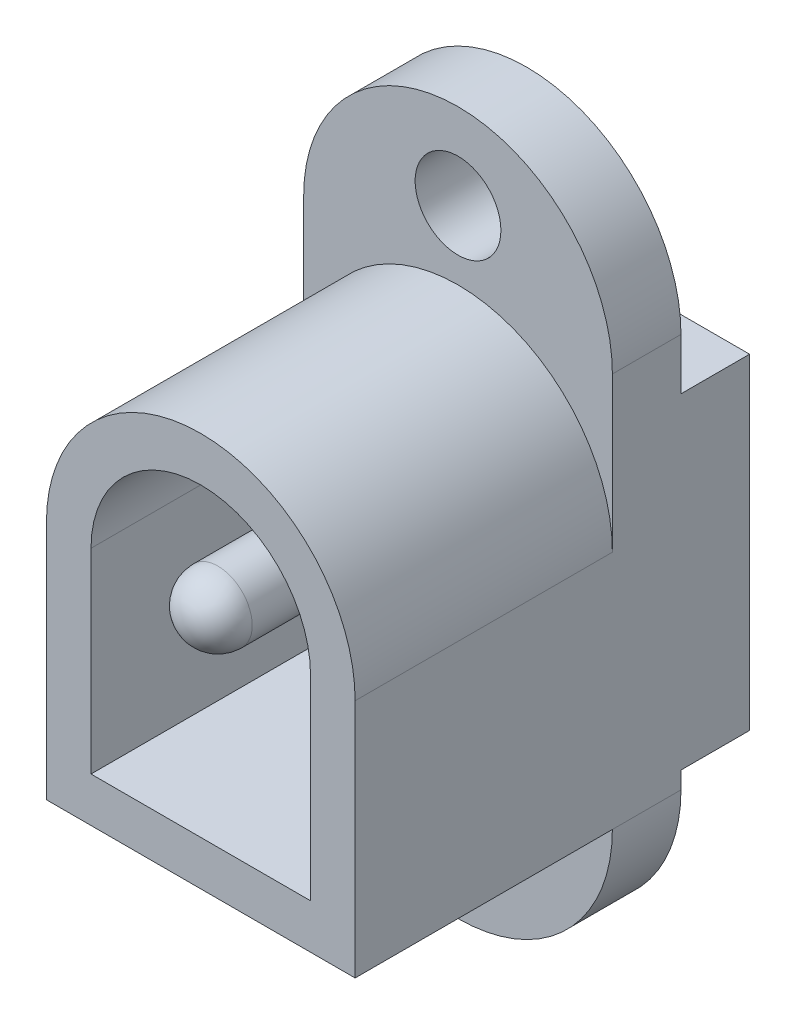
SolidWorks part; units mm, degrees
ref_plane "Piano frontale" through (0, 0, 0) normal (0, 0, 1) x (1, 0, 0)
ref_plane "Piano superiore" through (0, 0, 0) normal (0, 1, 0) x (1, 0, 0)
ref_plane "Piano destro" through (0, 0, 0) normal (1, 0, 0) x (0, 0, -1)
sketch "Schizzo1" plane through (0, 0, 0) normal (0, 0, 1) x (1, 0, 0)
  line L1 (4.5, -5.75) -> (-4.5, -5.75)
  line L2 (4.5, -5.75) -> (4.5, 5.75)
  line L3 (4.5, 5.75) -> (-4.5, 5.75)
  line L4 (-4.5, -5.75) -> (-4.5, 5.75)
  line L5 (4.5, -5.75) -> (-4.5, 5.75) construction
  line L6 (4.5, 5.75) -> (-4.5, -5.75) construction
  point P0 (0, 0)
  dimension "D1" = 9
  dimension "D2" = 11.5
extrude "Estrusione-Estrusione1" add sketch "Schizzo1" along normal blind 2
sketch "Schizzo2" plane through (0, 0, 2) normal (0, 0, 1) x (1, 0, 0)
  line L0 (0, 5.75) -> (0, -5.75) construction
  line L1 (4.5, 5.75) -> (-4.5, 5.75) construction
  line L2 (-4.5, -5.75) -> (4.5, -5.75) construction
  circle A0 centre (0, 5.75) radius 4.5
  circle A1 centre (0, -5.75) radius 4.5
extrude "Estrusione-Estrusione2" add sketch "Schizzo2" against normal blind 2
sketch "Schizzo3" plane through (0, 0, 2) normal (0, 0, 1) x (1, 0, 0)
  line L0 (0, 10.25) -> (0, -10.25) construction
  arc A0 (4.5, 5.75) -> (-4.5, 5.75) centre (0, 5.75) ccw construction
  arc A1 (-4.5, -5.75) -> (4.5, -5.75) centre (0, -5.75) ccw construction
  circle A2 centre (0, -7.75) radius 1.25
  circle A3 centre (0, 7.75) radius 1.25
  dimension "D3" = 2.5
  dimension "D4" = 2.5
  dimension "D1" = 7.75
  dimension "D2" = 7.75
extrude "Taglio-Estrusione1" cut sketch "Schizzo3" against normal blind 2
sketch "Schizzo4" plane through (0, 0, 2) normal (0, 0, 1) x (1, 0, 0)
  line L0 (-4.5, -5.75) -> (4.5, -5.75)
  line L1 (4.5, -5.75) -> (4.5, 1.25)
  line L2 (4.5, -5.75) -> (4.5, 5.75) construction
  line L3 (4.5, 1.25) -> (-4.5, 1.25)
  line L4 (-4.5, 5.75) -> (-4.5, -5.75) construction
  line L5 (-4.5, 1.25) -> (-4.5, -5.75)
  line L6 (-4.5, 1.25) -> (-4.5, -5.75)
  circle A0 centre (0, 1.25) radius 4.5
  line M3 (-4.5, 5.75) -> (-4.5, -5.75)
  line M5 (4.5, -5.75) -> (4.5, 5.75)
  dimension "D1" = 7
extrude "Estrusione-Estrusione4" add sketch "Schizzo4" along normal blind 7.5 contours L3 A0 | L3 A0 | A0 L0 M3 M5
sketch "Schizzo6" plane through (0, 0, 9.5) normal (0, 0, 1) x (1, 0, 0)
  line L0 (-4.5, 1.25) -> (4.5, 1.25) construction
  line L1 (4.5, -5.75) -> (4.5, 1.25) construction
  line L2 (-4.5, -5.75) -> (4.5, -5.75) construction
  line L3 (-3.2, 1.25) -> (3.2, 1.25)
  line L4 (-3.2, 1.25) -> (-3.2, -4.45)
  line L5 (-3.2, -4.45) -> (3.2, -4.45)
  line L6 (3.2, 1.25) -> (3.2, -4.45)
  line L7 (-4.5, 1.25) -> (-4.5, -5.75) construction
  arc A0 (4.5, 1.25) -> (-4.5, 1.25) centre (0, 1.25) ccw construction
  circle A1 centre (0, 1.25) radius 3.2
  dimension "D1" = 1.3
  dimension "D2" = 1.3
  dimension "D3" = 1.3
extrude "Taglio-Estrusione2" cut sketch "Schizzo6" against normal blind 7.5 contours L3 A1 | L3 A1 | A1 L4 L5 L6
sketch "Schizzo7" plane through (0, 0, 2) normal (0, 0, 1) x (1, 0, 0)
  line L0 (0, 4.45) -> (0, -4.45) construction
  line L1 (-3.2, -4.45) -> (3.2, -4.45) construction
  arc A0 (3.2, 1.25) -> (-3.2, 1.25) centre (0, 1.25) ccw construction
  circle A1 centre (0, 1.15) radius 1
  dimension "D2" = 2
  dimension "D1" = 3.3
extrude "Estrusione-Estrusione5" add sketch "Schizzo7" along normal blind 8
fillet "Raccordo1" radius 1 1 edges at (1, 1.15, 10)
sketch "Schizzo8" plane through (0, 0, 0) normal (0, 0, -1) x (-1, 0, 0)
  line L0 (-4.5, -5.75) -> (-4.5, 5.75) construction
  line L1 (-4.5, -5.25) -> (4.5, -5.25)
  line L2 (-4.5, -5.25) -> (-4.5, 4.25)
  line L3 (-4.5, 4.25) -> (4.5, 4.25)
  line L4 (4.5, -5.25) -> (4.5, 4.25)
  line L5 (4.5, 5.75) -> (4.5, -5.75) construction
  arc A0 (-4.5, -5.75) -> (4.5, -5.75) centre (0, -5.75) ccw construction
  arc A1 (4.5, 5.75) -> (-4.5, 5.75) centre (0, 5.75) ccw construction
  point P11 (0, -10.25)
  point P12 (0, 10.25)
  dimension "D1" = 5
  dimension "D2" = 6
extrude "Estrusione-Estrusione6" add sketch "Schizzo8" along normal blind 2
sketch "Schizzo10" plane through (0, 0, 0) normal (0, 0, -1) x (-1, 0, 0)
  line L0 (0, 10.25) -> (0, -10.25) construction
  arc A0 (4.5, 5.75) -> (-4.5, 5.75) centre (0, 5.75) ccw construction
  arc A1 (-4.5, -5.75) -> (4.5, -5.75) centre (0, -5.75) ccw construction
